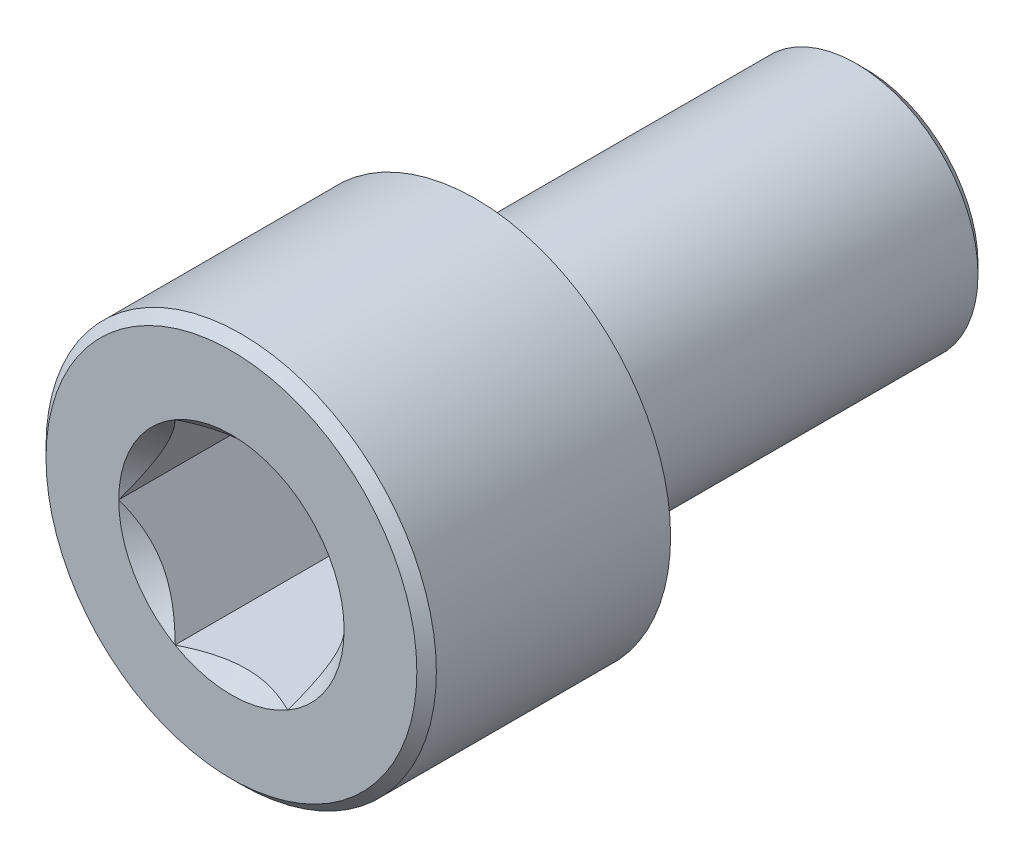
SolidWorks part; units mm, degrees
ref_plane "Спереди" through (0, 0, 0) normal (0, 0, 1) x (1, 0, 0)
ref_plane "Сверху" through (0, 0, 0) normal (0, 1, 0) x (1, 0, 0)
ref_plane "Справа" through (0, 0, 0) normal (1, 0, 0) x (0, 0, -1)
sketch "Эскиз1" plane through (0, 0, 0) normal (0, 0, 1) x (1, 0, 0)
  circle A0 centre (0, 0) radius 4
extrude "Бобышка-Вытянуть1" add sketch "Эскиз1" along normal blind 5
sketch "Эскиз2" plane through (0, 0, 5) normal (0, 0, 1) x (1, 0, 0)
  line L1 (2.3094, 0) -> (1.1547, 2)
  line L2 (1.1547, 2) -> (-1.1547, 2)
  line L3 (-1.1547, 2) -> (-2.3094, 0)
  line L4 (-2.3094, 0) -> (-1.1547, -2)
  line L5 (-1.1547, -2) -> (1.1547, -2)
  line L6 (1.1547, -2) -> (2.3094, 0)
  circle A0 centre (0, 0) radius 2 construction
extrude "Вырез-Вытянуть1" cut sketch "Эскиз2" against normal blind 3.4
sketch "Эскиз3" plane through (0, 0, 5) normal (0, 0, 1) x (1, 0, 0)
  circle A0 centre (0, 0) radius 2.3094
extrude "Вырез-Вытянуть2" cut sketch "Эскиз3" against normal blind 3.4 draft 45
chamfer "Фаска1" distance 0.2 angle 45 1 edges at (4, 0, 5)
sketch "Эскиз4" plane through (0, 0, 0) normal (0, 0, -1) x (-1, 0, 0)
  circle A0 centre (0, 0) radius 2.5
extrude "Бобышка-Вытянуть2" add sketch "Эскиз4" along normal blind 8
chamfer "Фаска2" distance 0.2 angle 45 1 edges at (-2.5, 0, -8)
